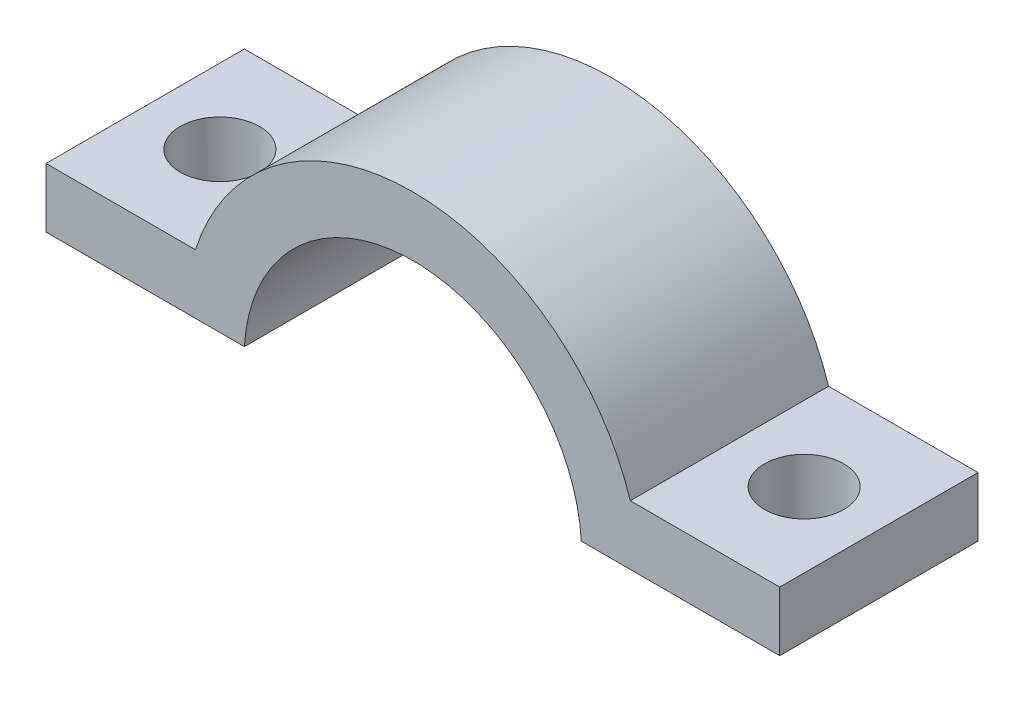
SolidWorks part; units mm, degrees
ref_plane "Front Plane" through (0, 0, 0) normal (0, 0, 1) x (1, 0, 0)
ref_plane "Top Plane" through (0, 0, 0) normal (0, 1, 0) x (1, 0, 0)
ref_plane "Right Plane" through (0, 0, 0) normal (1, 0, 0) x (0, 0, -1)
sketch "Sketch1" plane through (0, 0, 0) normal (0, 0, 1) x (1, 0, 0)
  line L0 (8.4953, 0.5) -> (18.5, 0.5)
  line L1 (-18.5, 3.5002) -> (-18.5, 0.5)
  line L2 (18.5, 3.5002) -> (18.5, 0.5)
  line L3 (0, 0) -> (0, 14.2591) construction
  line L4 (10.9649, 3.5002) -> (18.5, 3.5002)
  line L5 (-10.9649, 3.5002) -> (-18.5, 3.5002)
  line L6 (-8.4953, 0.5) -> (-18.5, 0.5)
  line L7 (0, 0) -> (-8.1388, 8.1388) construction
  line L8 (18.5, 0.5) -> (18.5, 0) construction
  line L9 (8.1388, 8.1388) -> (0, 0) construction
  line L10 (18.5, 0) -> (-18.5, 0) construction
  line L11 (-18.5, 0) -> (-18.5, 0.5) construction
  line L12 (-8.4953, 0.5) -> (8.4953, 0.5) construction
  arc A0 (8.4953, 0.5) -> (-8.4953, 0.5) centre (0, 0) ccw
  arc A1 (10.9649, 3.5002) -> (-10.9649, 3.5002) centre (0, 0) ccw
  point P16 (8.1388, 8.1388)
  point P17 (-8.1388, 8.1388)
  dimension "D1" = 8.51
  dimension "D2" = 3
  dimension "D3" = 0.5
  dimension "D4" = 45
  dimension "D5" = 18.5
  dimension "D6" = 45
  dimension "D8" = 3.0002
  dimension "D9" = 90
extrude "Boss-Extrude1" add sketch "Sketch1" along normal blind 10
sketch "Sketch2" plane through (0, 0, 0) normal (0, 1, 0) x (1, 0, 0)
  line L0 (-18.5, 0) -> (-10.9649, -10) construction
  line L1 (-10.9649, -10) -> (-18.5, -10) construction
  line L2 (0, 0) -> (0, -10) construction
  line L3 (-10.9649, -10) -> (10.9649, -10) construction
  circle A0 centre (-14.7324, -5) radius 2
  circle A1 centre (14.7324, -5) radius 2
  point P7 (-14.7324, -10)
  dimension "D1" = 4
  dimension "D2" = 5
extrude "Cut-Extrude3" cut sketch "Sketch2" along normal up to next
